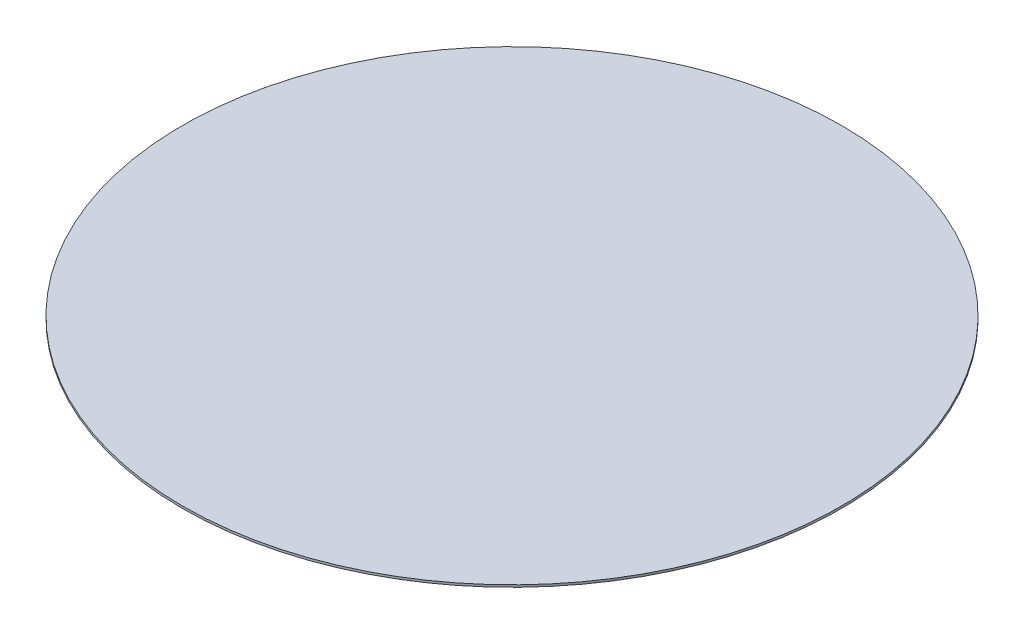
SolidWorks part; units mm, degrees
ref_plane "Front Plane" through (0, 0, 0) normal (0, 0, 1) x (1, 0, 0)
ref_plane "Top Plane" through (0, 0, 0) normal (0, 1, 0) x (1, 0, 0)
ref_plane "Right Plane" through (0, 0, 0) normal (1, 0, 0) x (0, 0, -1)
sketch "Sketch1" plane through (0, 0, 0) normal (0, 1, 0) x (1, 0, 0)
  circle A0 centre (0, 0) radius 150
  dimension "D1" = 300
extrude "Boss-Extrude1" add sketch "Sketch1" along normal blind 1
